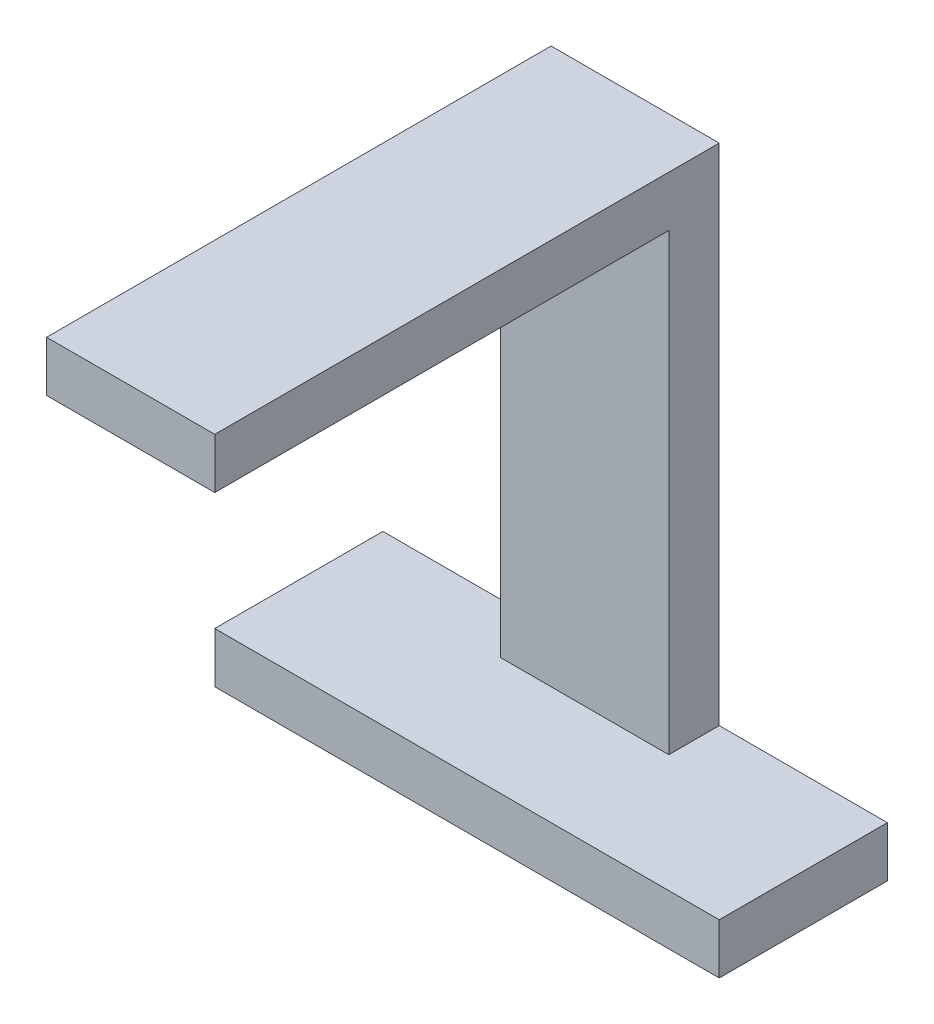
SolidWorks part; units mm, degrees
ref_plane "前视基准面" through (0, 0, 0) normal (0, 0, 1) x (1, 0, 0)
ref_plane "上视基准面" through (0, 0, 0) normal (0, 1, 0) x (1, 0, 0)
ref_plane "右视基准面" through (0, 0, 0) normal (1, 0, 0) x (0, 0, -1)
sketch "草图2" plane through (0, 0, 0) normal (1, 0, 0) x (0, 0, -1)
  line L0 (-15.351, 50.7489) -> (14.649, 50.7489)
  line L1 (14.649, 50.7489) -> (14.649, 20.7489)
  line L2 (14.649, 20.7489) -> (11.649, 20.7489)
  line L3 (11.649, 20.7489) -> (11.649, 47.7502)
  line L4 (11.649, 47.7502) -> (-15.351, 47.7502)
  line L5 (-15.351, 47.7502) -> (-15.351, 50.7489)
extrude "凸台-拉伸2" add sketch "草图2" along normal blind 10
sketch "草图4" plane through (0, 20.7489, 0) normal (0, -1, 0) x (1, 0, 0)
  line L0 (10, -14.649) -> (-10, -14.649)
  line L1 (-10, -14.649) -> (-10, -4.649)
  line L2 (-10, -4.649) -> (10, -4.649)
  line L3 (10, 15.351) -> (10, -11.649) construction
  line L4 (10, -4.649) -> (20, -4.649)
  line L5 (20, -4.649) -> (20, -14.649)
  line L6 (20, -14.649) -> (10, -14.649)
extrude "凸台-拉伸3" add sketch "草图4" along normal blind 3
